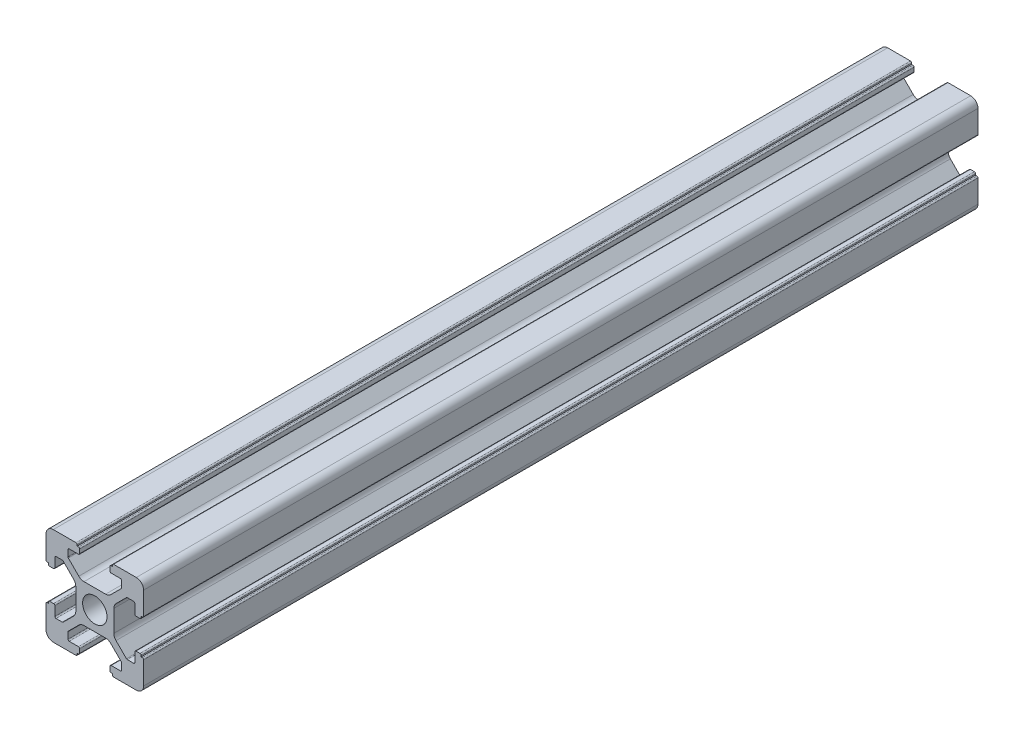
SolidWorks part; units mm, degrees
material "1060 Alloy"
ref_plane "前视基准面" through (0, 0, 0) normal (0, 0, 1) x (1, 0, 0)
ref_plane "上视基准面" through (0, 0, 0) normal (0, 1, 0) x (1, 0, 0)
ref_plane "右视基准面" through (0, 0, 0) normal (1, 0, 0) x (0, 0, -1)
sketch "草图1" plane through (0, 0, 0) normal (0, 0, 1) x (1, 0, 0)
  line L0 (0, 0) -> (0, 5.5) construction
  line L1 (-8.5023, -10.0023) -> (-3.85, -10.0023)
  line L2 (-10.0023, -8.5023) -> (-10.0023, -3.85)
  line L3 (-8.5023, 10.0023) -> (-3.85, 10.0023)
  line L4 (10.0023, -8.5023) -> (10.0023, -3.85)
  line L5 (-10.0023, -10.0023) -> (10.0023, 10.0023) construction
  line L6 (-10.0023, 10.0023) -> (10.0023, -10.0023) construction
  line L7 (-2.218, -3.9) -> (2.218, -3.9)
  line L8 (-3.9, -2.218) -> (-3.9, 2.218)
  line L9 (-2.218, 3.9) -> (2.218, 3.9)
  line L10 (3.9, -2.218) -> (3.9, 2.218)
  line L11 (-3.9, -3.9) -> (3.9, 3.9) construction
  line L12 (-3.9, 3.9) -> (3.9, -3.9) construction
  line L13 (-5.25, -8.2) -> (-3.35, -8.2)
  line L14 (-8.2, -5.25) -> (-8.2, -3.35)
  line L15 (-5.25, 8.2) -> (-3.35, 8.2)
  line L16 (8.2, -5.25) -> (8.2, -3.35)
  line L17 (-8.2, -8.2) -> (8.2, 8.2) construction
  line L18 (-8.2, 8.2) -> (8.2, -8.2) construction
  line L19 (-7.95, 5.5) -> (-6.6642, 5.5)
  line L20 (0, 0) -> (5.5, 0) construction
  line L23 (-5.5, 7.95) -> (-5.5, 6.6642)
  line L26 (0, 0) -> (-0.5303, 0.5303)
  line L27 (3.2787, 4.3393) -> (5.4268, 6.4874)
  line L28 (0, 0) -> (0.5303, -0.5303)
  line L29 (5.5, 6.6642) -> (5.5, 7.95)
  line L30 (4.3393, 3.2787) -> (6.4874, 5.4268)
  line L31 (6.6642, 5.5) -> (7.95, 5.5)
  line L32 (4.3393, -3.2787) -> (6.4874, -5.4268)
  line L33 (3.2787, -4.3393) -> (5.4268, -6.4874)
  line L34 (-3.2787, -4.3393) -> (-5.4268, -6.4874)
  line L35 (-4.3393, -3.2787) -> (-6.4874, -5.4268)
  line L36 (-4.3393, 3.2787) -> (-6.4874, 5.4268)
  line L37 (-3.2787, 4.3393) -> (-5.4268, 6.4874)
  line L38 (3.1, -8.45) -> (3.1, -9.2523)
  line L39 (8.45, 3.1) -> (9.2523, 3.1)
  line L40 (-5.5, -6.6642) -> (-5.5, -7.95)
  line L41 (-6.6642, -5.5) -> (-7.95, -5.5)
  line L42 (5.5, -6.6642) -> (5.5, -7.95)
  line L43 (6.6642, -5.5) -> (7.95, -5.5)
  line L44 (9.2523, -3.1) -> (8.45, -3.1)
  line L46 (10.0023, 3.85) -> (10.0023, 8.5023)
  line L47 (8.2, 3.35) -> (8.2, 5.25)
  line L48 (-3.1, -9.2523) -> (-3.1, -8.45)
  line L49 (-8.45, -3.1) -> (-9.2523, -3.1)
  line L50 (-9.2523, 3.1) -> (-8.45, 3.1)
  line L51 (-3.1, 8.45) -> (-3.1, 9.2523)
  line L52 (3.1, 9.2523) -> (3.1, 8.45)
  line L53 (3.85, 10.0023) -> (8.5023, 10.0023)
  line L54 (3.35, 8.2) -> (5.25, 8.2)
  line L55 (-10.0023, 3.85) -> (-10.0023, 8.5023)
  line L56 (-8.2, 3.35) -> (-8.2, 5.25)
  line L57 (3.35, -8.2) -> (5.25, -8.2)
  line L58 (3.85, -10.0023) -> (8.5023, -10.0023)
  line L59 (9.7523, -3.6) -> (9.5023, -3.6)
  line L61 (9.7523, 3.6) -> (9.5023, 3.6)
  line L62 (9.5023, -3.6) -> (9.5023, -3.35)
  line L63 (3.6, -9.7523) -> (3.6, -9.5023)
  line L64 (3.35, -9.5023) -> (3.6, -9.5023)
  line L65 (9.5023, 3.35) -> (9.5023, 3.6)
  line L66 (-3.6, -9.5023) -> (-3.35, -9.5023)
  line L67 (-3.6, -9.7523) -> (-3.6, -9.5023)
  line L68 (-9.7523, -3.6) -> (-9.5023, -3.6)
  line L69 (-9.5023, -3.35) -> (-9.5023, -3.6)
  line L70 (-9.5023, 3.6) -> (-9.5023, 3.35)
  line L71 (-9.7523, 3.6) -> (-9.5023, 3.6)
  line L72 (-3.6, 9.7523) -> (-3.6, 9.5023)
  line L73 (-3.35, 9.5023) -> (-3.6, 9.5023)
  line L74 (3.6, 9.5023) -> (3.35, 9.5023)
  line L75 (3.6, 9.7523) -> (3.6, 9.5023)
  circle A0 centre (0, 0) radius 2.5
  arc A1 (10.0023, 8.5023) -> (8.5023, 10.0023) centre (8.5023, 8.5023) ccw
  arc A2 (8.5023, -10.0023) -> (10.0023, -8.5023) centre (8.5023, -8.5023) ccw
  arc A3 (-10.0023, -8.5023) -> (-8.5023, -10.0023) centre (-8.5023, -8.5023) ccw
  arc A4 (-10.0023, 8.5023) -> (-8.5023, 10.0023) centre (-8.5023, 8.5023) cw
  arc A5 (-9.5023, -3.35) -> (-9.2523, -3.1) centre (-9.2523, -3.35) cw
  arc A6 (-9.7523, -3.6) -> (-10.0023, -3.85) centre (-9.7523, -3.85) ccw
  arc A7 (-8.45, -3.1) -> (-8.2, -3.35) centre (-8.45, -3.35) cw
  arc A8 (-7.95, -5.5) -> (-8.2, -5.25) centre (-7.95, -5.25) cw
  arc A9 (-6.4874, -5.4268) -> (-6.6642, -5.5) centre (-6.6642, -5.25) cw
  arc A10 (-5.4268, -6.4874) -> (-5.5, -6.6642) centre (-5.25, -6.6642) ccw
  arc A11 (-5.5, -7.95) -> (-5.25, -8.2) centre (-5.25, -7.95) ccw
  arc A12 (-3.6, -9.7523) -> (-3.85, -10.0023) centre (-3.85, -9.7523) cw
  arc A13 (-3.35, -9.5023) -> (-3.1, -9.2523) centre (-3.35, -9.2523) ccw
  arc A14 (-3.1, -8.45) -> (-3.35, -8.2) centre (-3.35, -8.45) ccw
  arc A15 (3.1, -8.45) -> (3.35, -8.2) centre (3.35, -8.45) cw
  arc A16 (5.5, -7.95) -> (5.25, -8.2) centre (5.25, -7.95) cw
  arc A17 (5.4268, -6.4874) -> (5.5, -6.6642) centre (5.25, -6.6642) cw
  arc A18 (6.4874, -5.4268) -> (6.6642, -5.5) centre (6.6642, -5.25) ccw
  arc A19 (7.95, -5.5) -> (8.2, -5.25) centre (7.95, -5.25) ccw
  arc A20 (8.45, -3.1) -> (8.2, -3.35) centre (8.45, -3.35) ccw
  arc A21 (9.5023, -3.35) -> (9.2523, -3.1) centre (9.2523, -3.35) ccw
  arc A22 (9.7523, -3.6) -> (10.0023, -3.85) centre (9.7523, -3.85) cw
  arc A23 (3.35, -9.5023) -> (3.1, -9.2523) centre (3.35, -9.2523) cw
  arc A24 (3.6, -9.7523) -> (3.85, -10.0023) centre (3.85, -9.7523) ccw
  arc A25 (7.95, 5.5) -> (8.2, 5.25) centre (7.95, 5.25) cw
  arc A26 (8.2, 3.35) -> (8.45, 3.1) centre (8.45, 3.35) ccw
  arc A27 (9.5023, 3.35) -> (9.2523, 3.1) centre (9.2523, 3.35) cw
  arc A28 (9.7523, 3.6) -> (10.0023, 3.85) centre (9.7523, 3.85) ccw
  arc A29 (6.6642, 5.5) -> (6.4874, 5.4268) centre (6.6642, 5.25) ccw
  arc A30 (5.4268, 6.4874) -> (5.5, 6.6642) centre (5.25, 6.6642) ccw
  arc A31 (5.5, 7.95) -> (5.25, 8.2) centre (5.25, 7.95) ccw
  arc A32 (3.1, 8.45) -> (3.35, 8.2) centre (3.35, 8.45) ccw
  arc A33 (3.6, 9.7523) -> (3.85, 10.0023) centre (3.85, 9.7523) cw
  arc A34 (3.35, 9.5023) -> (3.1, 9.2523) centre (3.35, 9.2523) ccw
  arc A35 (-9.7523, 3.6) -> (-10.0023, 3.85) centre (-9.7523, 3.85) cw
  arc A36 (-9.5023, 3.35) -> (-9.2523, 3.1) centre (-9.2523, 3.35) ccw
  arc A37 (-8.45, 3.1) -> (-8.2, 3.35) centre (-8.45, 3.35) ccw
  arc A38 (-8.2, 5.25) -> (-7.95, 5.5) centre (-7.95, 5.25) cw
  arc A39 (-6.4874, 5.4268) -> (-6.6642, 5.5) centre (-6.6642, 5.25) ccw
  arc A40 (-5.4268, 6.4874) -> (-5.5, 6.6642) centre (-5.25, 6.6642) cw
  arc A41 (-5.5, 7.95) -> (-5.25, 8.2) centre (-5.25, 7.95) cw
  arc A42 (-3.1, 8.45) -> (-3.35, 8.2) centre (-3.35, 8.45) cw
  arc A43 (-3.1, 9.2523) -> (-3.35, 9.5023) centre (-3.35, 9.2523) ccw
  arc A44 (-3.6, 9.7523) -> (-3.85, 10.0023) centre (-3.85, 9.7523) ccw
  arc A45 (-4.3393, 3.2787) -> (-3.9, 2.218) centre (-5.4, 2.218) cw
  arc A46 (-3.2787, 4.3393) -> (-2.218, 3.9) centre (-2.218, 5.4) ccw
  arc A47 (3.2787, 4.3393) -> (2.218, 3.9) centre (2.218, 5.4) cw
  arc A48 (4.3393, 3.2787) -> (3.9, 2.218) centre (5.4, 2.218) ccw
  arc A49 (4.3393, -3.2787) -> (3.9, -2.218) centre (5.4, -2.218) cw
  arc A50 (3.2787, -4.3393) -> (2.218, -3.9) centre (2.218, -5.4) ccw
  arc A51 (-4.3393, -3.2787) -> (-3.9, -2.218) centre (-5.4, -2.218) ccw
  arc A52 (-2.218, -3.9) -> (-3.2787, -4.3393) centre (-2.218, -5.4) ccw
  point P0 (0, 0)
  point P7 (10.0023, 0)
  point P62 (0, 0)
  point P76 (0, 0)
  point P92 (-8.2, -5.5)
  point P99 (0, 0)
  point P106 (-5.5, -8.2)
  point P117 (5.5, -8.2)
  point P124 (8.2, -5.5)
  point P137 (8.2, 5.5)
  point P140 (8.2, 3.1)
  point P147 (6.5607, 5.5)
  point P152 (5.5, 8.2)
  point P167 (-8.2, 5.5)
  point P174 (-5.5, 8.2)
  dimension "D1" = 1.5
  dimension "D5" = 0.25
  dimension "D6" = 1.5
  dimension "D2" = 4
  dimension "D3" = 4
  dimension "D4" = 4
extrude "凸台-拉伸1" add sketch "草图1" along normal blind 171 contours A52 L7 A50 L33 A17 L42 A16 L57 A15 L38 A23 L64 L63 A24 L58 A2 L4 A22 L59 L62 A21 L44 A20 L16 A19 L43 A18 L32 A49 L10 A48 L30 A29 L31 A25 L47 A26 L39 A27 L65 L61 A28 L46 A1 L53 A33 L75 L74 A34 L52 A32
ref_plane "Plane1" through (0, 0, 85.5) normal (0, 0, 1) x (1, 0, 0)
